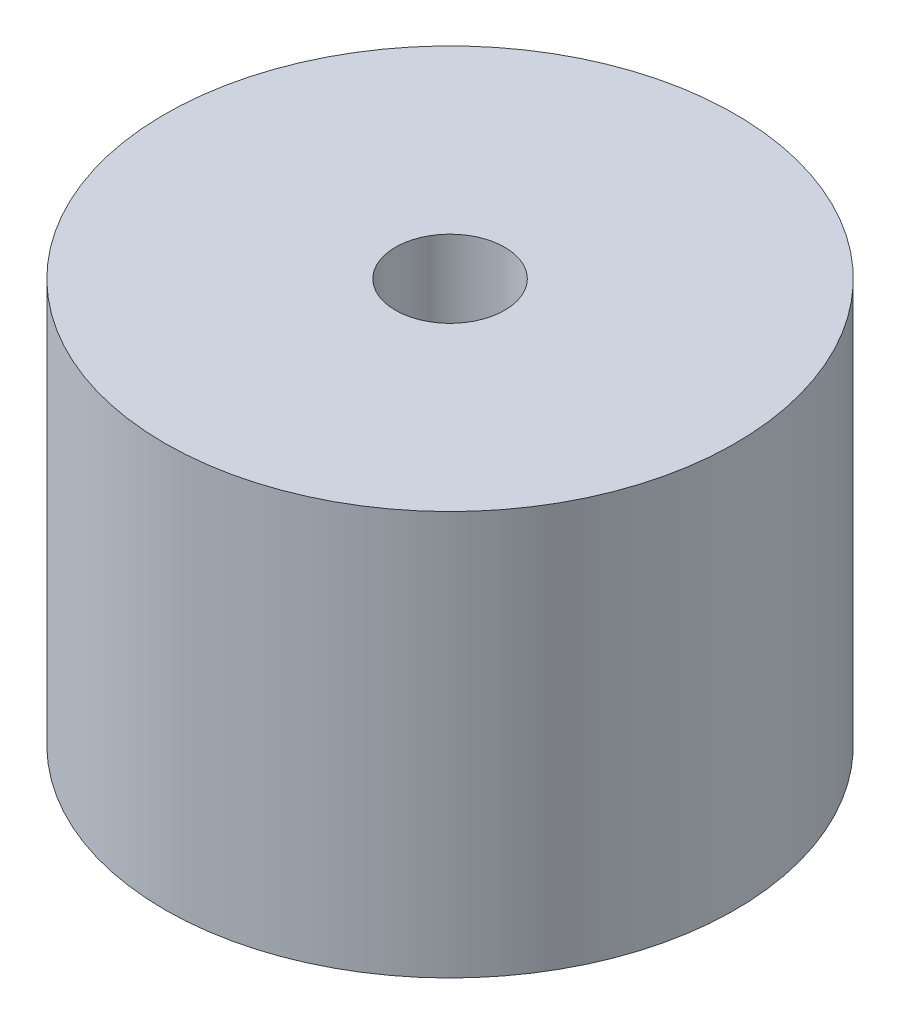
SolidWorks part; units mm, degrees
ref_plane "Front Plane" through (0, 0, 0) normal (0, 0, 1) x (1, 0, 0)
ref_plane "Top Plane" through (0, 0, 0) normal (0, 1, 0) x (1, 0, 0)
ref_plane "Right Plane" through (0, 0, 0) normal (1, 0, 0) x (0, 0, -1)
sketch "Sketch1" plane through (0, 0, 0) normal (0, 1, 0) x (1, 0, 0)
  circle A0 centre (0, 0) radius 6
  dimension "D1" = 12
extrude "Boss-Extrude1" add sketch "Sketch1" along normal blind 8.5
sketch "Sketch2" plane through (0, 8.5, 0) normal (0, 1, 0) x (1, 0, 0)
  circle A0 centre (0, 0) radius 1.15
  dimension "D1" = 2.3
extrude "Cut-Extrude1" cut sketch "Sketch2" against normal blind 3
